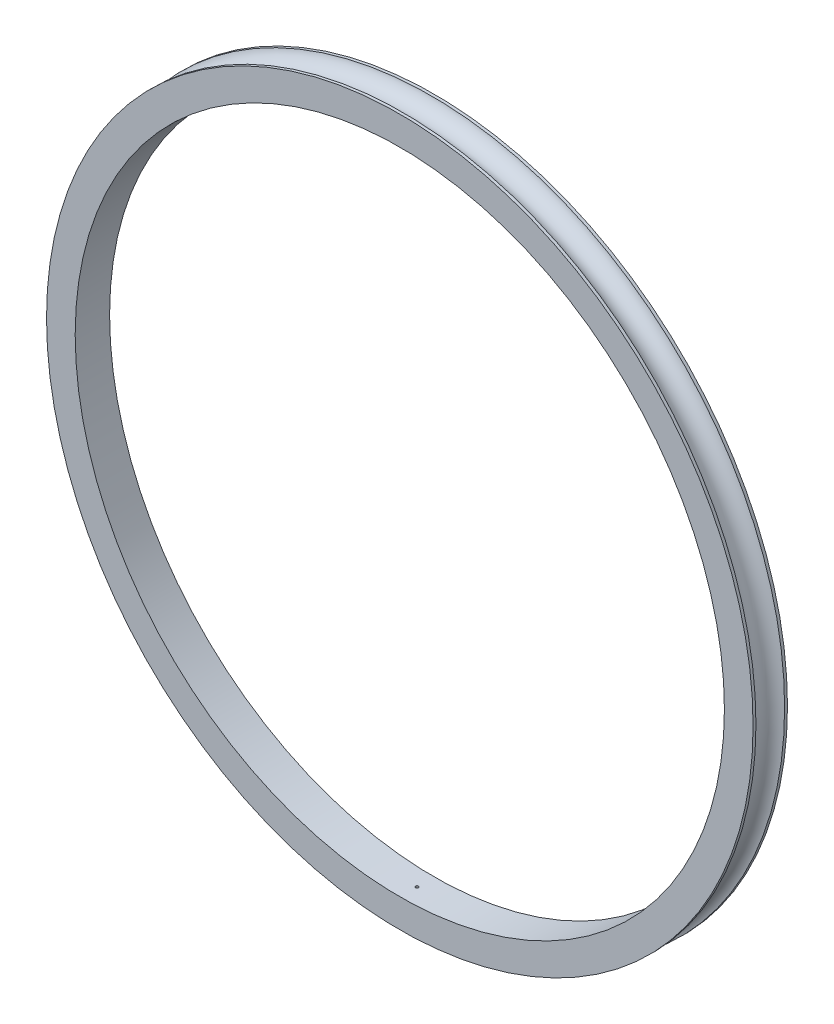
SolidWorks part; units mm, degrees
ref_plane "Front Plane" through (0, 0, 0) normal (0, 0, 1) x (1, 0, 0)
ref_plane "Top Plane" through (0, 0, 0) normal (0, 1, 0) x (1, 0, 0)
ref_plane "Right Plane" through (0, 0, 0) normal (1, 0, 0) x (0, 0, -1)
sketch "Sketch1" plane through (0, 0, 0) normal (1, 0, 0) x (0, 0, -1)
  line L0 (0, 84.8002) -> (0, -101.7881) construction
  line L1 (0.5, 113.2472) -> (6, 113.2472)
  line L2 (6, 113.2472) -> (6, 123.2472)
  line L4 (-6, 123.2472) -> (-6, 113.2472)
  line L5 (-6, 113.2472) -> (-0.5, 113.2472)
  line L9 (-80.7858, 0) -> (85.9776, 0) construction
  line L10 (-6, 123.2472) -> (-5, 123.2472)
  line L11 (6, 123.2472) -> (5, 123.2472)
  line L12 (0.5, 113.2472) -> (-0.5, 113.2472)
  arc A3 (-5, 123.2472) -> (5, 123.2472) centre (0, 124.3722) ccw
  point P1 (0, 113.2472)
  point P5 (0, 119.2472)
  point P10 (0, 0)
  point P12 (0, 113.2472)
  dimension "D7" = 10
  dimension "D1" = 113.2472
  dimension "D5" = 6
  dimension "D6" = 6
  dimension "D8" = 4
  dimension "D9" = 10
revolve "Revolve1" add sketch "Sketch1" angle 360 about L9
ref_plane "Plane1" through (0, 113.2472, 0) normal (0, -1, 0) x (-1, 0, 0)
ref_plane "Plane2" through (0, 115.2472, 0) normal (0, -1, 0) x (-1, 0, 0)
sketch "Sketch3" plane through (0, 115.2472, 0) normal (0, -1, 0) x (-1, 0, 0)
  circle A0 centre (0, 0) radius 0.5
extrude "Cut-Extrude1" cut sketch "Sketch3" along normal blind 29
ref_plane "Plane3" through (0, -113.2472, 0) normal (0, 1, 0) x (1, 0, 0)
ref_plane "Plane4" through (0, -115.2472, 0) normal (0, 1, 0) x (1, 0, 0)
sketch "Sketch4" plane through (0, -115.2472, 0) normal (0, 1, 0) x (1, 0, 0)
  circle A0 centre (0, 0) radius 0.5
extrude "Cut-Extrude2" cut sketch "Sketch4" along normal blind 11
